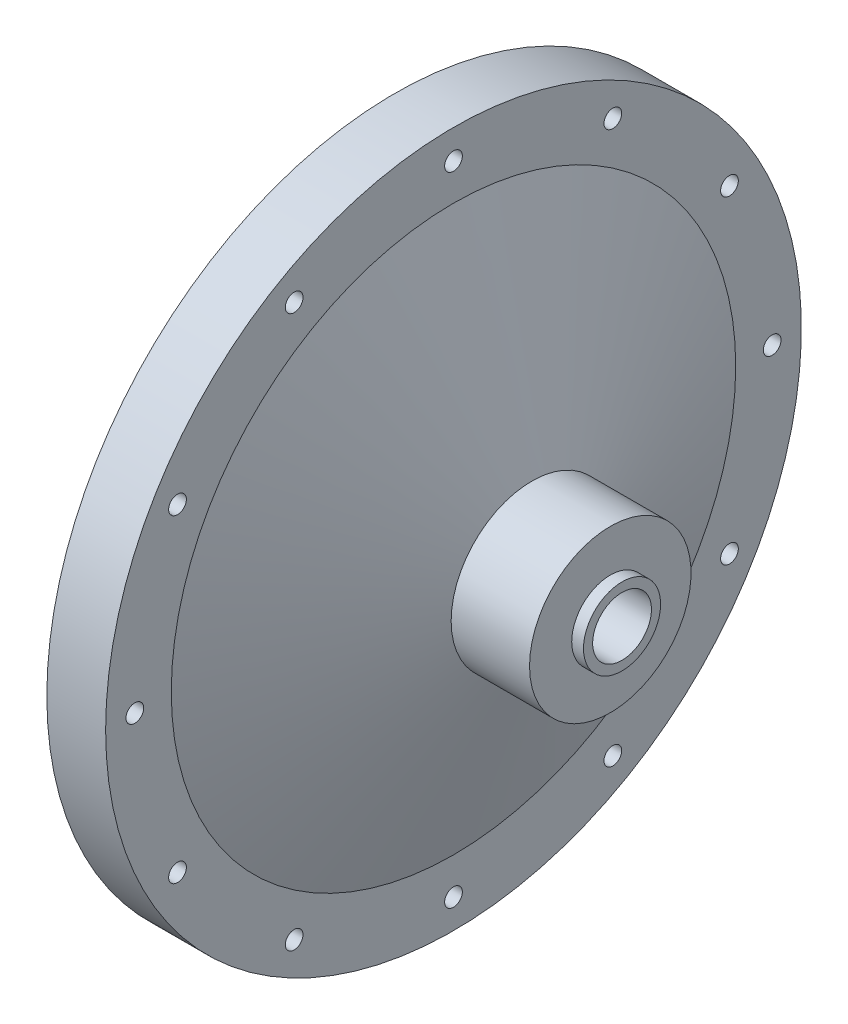
SolidWorks part; units mm, degrees
material "7075-T6 (SN)"
ref_plane "Front Plane" through (0, 0, 0) normal (0, 0, 1) x (1, 0, 0)
ref_plane "Top Plane" through (0, 0, 0) normal (0, 1, 0) x (1, 0, 0)
ref_plane "Right Plane" through (0, 0, 0) normal (1, 0, 0) x (0, 0, -1)
sketch "Sketch2" plane through (0, 0, 0) normal (0, 0, 1) x (1, 0, 0)
  line L0 (0, 0) -> (165.0115, 0) construction
  line L1 (0, 0) -> (0, 56.3562)
  line L2 (0, 56.3562) -> (9.525, 56.3562)
  line L3 (9.525, 56.3562) -> (9.525, 45.72)
  line L4 (9.525, 45.72) -> (22.225, 13.081)
  line L5 (34.925, 13.081) -> (34.925, 6.2484)
  line L6 (22.225, 13.081) -> (34.925, 13.081)
  line L7 (34.925, 6.2484) -> (36.83, 6.2484)
  line L8 (36.83, 6.2484) -> (36.83, 0)
  line L9 (0, 0) -> (36.83, 0)
  dimension "D1" = 56.3562
  dimension "D2" = 9.525
  dimension "D3" = 45.72
  dimension "D4" = 13.081
  dimension "D5" = 12.7
  dimension "D6" = 12.7
  dimension "D7" = 6.2484
  dimension "D8" = 1.905
revolve "Main Structure" add sketch "Sketch2" angle 360 about L0
cosmetic thread "Cosmetic Thread1" parameters "D2"=23.1953
sketch "Sketch3" plane through (36.83, 0, 0) normal (1, 0, 0) x (0, 0, -1)
  circle A0 centre (0, 0) radius 4.7625
  dimension "D1" = 9.525
extrude "Oxidizer Inlet Hole" cut sketch "Sketch3" against normal through all
sketch "Sketch4" plane through (0, 0, 0) normal (-1, 0, 0) x (0, 0, 1)
  circle A0 centre (0, 0) radius 51.6255 construction
  circle A1 centre (0, -51.6255) radius 2.146
  circle A2 centre (-25.8127, -44.709) radius 2.146
  circle A3 centre (-44.709, -25.8128) radius 2.146
  circle A4 centre (-51.6255, 0) radius 2.146
  circle A5 centre (-44.709, 25.8127) radius 2.146
  circle A6 centre (-25.8128, 44.709) radius 2.146
  circle A7 centre (0, 51.6255) radius 2.146
  circle A8 centre (25.8127, 44.709) radius 2.146
  circle A9 centre (44.709, 25.8128) radius 2.146
  circle A10 centre (51.6255, 0) radius 2.146
  circle A11 centre (44.709, -25.8127) radius 2.146
  circle A12 centre (25.8128, -44.709) radius 2.146
  point P29 (0, 0)
  dimension "D1" = 12
  dimension "D2" = 103.251
hole_wizard "Flange Holes" positions "Sketch7" profile "Sketch8" hole size "#33" standard "ANSI Inch" end condition up to next
sketch "Sketch7" plane through (0, 0, 0) normal (-1, 0, 0) x (0, 0, 1)
  point P0 (0, -51.6255)
  point P3 (-25.8127, -44.709)
  point P6 (-44.709, -25.8128)
  point P9 (-51.6255, 0)
  point P12 (-44.709, 25.8127)
  point P15 (-25.8128, 44.709)
  point P18 (0, 51.6255)
  point P21 (25.8127, 44.709)
  point P24 (44.709, 25.8128)
  point P27 (51.6255, 0)
  point P30 (44.709, -25.8127)
  point P33 (25.8128, -44.709)
sketch "Sketch8" plane through (0, -51.6255, 0) normal (0, 1, 0) x (0, 0, 1)
  line L0 (0, 0) -> (0, 9.525)
  line L1 (0, 9.525) -> (1.4351, 9.525)
  line L2 (1.4351, 9.525) -> (1.4351, 0)
  line L5 (1.4351, 0) -> (0, 0)
  line L11 (0, -6.35) -> (0, 107.95) construction
  dimension "Thru Hole Dia." = 2.8702
  dimension "Thru Hole Depth" = 9.525
sketch "Sketch9" plane through (0, 0, 0) normal (-1, 0, 0) x (0, 0, 1)
  line L0 (0, 0) -> (-67.6727, 18.1329) construction
  line L1 (0, 0) -> (-51.6255, 0) construction
  circle A0 centre (0, 0) radius 51.6255 construction
  circle A1 centre (-49.8664, 13.3617) radius 2.9451
  circle A2 centre (49.8664, -13.3617) radius 2.9451
  point P14 (0, 0)
  dimension "D1" = 15
  dimension "D2" = 2
hole_wizard "Dowel Holes" positions "Sketch10" profile "Sketch11" hole size "3/16" standard "ANSI Inch"
sketch "Sketch10" plane through (0, 0, 0) normal (-1, 0, 0) x (0, 0, 1)
  point P0 (49.8664, -13.3617)
  point P3 (-49.8664, 13.3617)
sketch "Sketch11" plane through (0, -13.3617, 49.8664) normal (0, 1, 0) x (0, 0, 1)
  line L0 (0, 0) -> (0, 7.7808)
  line L1 (0, 7.7808) -> (2.3812, 6.35)
  line L2 (2.3812, 6.35) -> (2.3812, 0)
  line L5 (2.3812, 0) -> (0, 0)
  line L10 (0, 7.7808) -> (-2.3812, 6.35) construction
  line L11 (0, -6.35) -> (0, 107.95) construction
  dimension "Hole Dia." = 4.7625
  dimension "Hole Depth" = 6.35
  dimension "Drill Angle" = 118
sketch "Sketch12" plane through (0, 0, 0) normal (-1, 0, 0) x (0, 0, 1)
  circle A0 centre (0, 0) radius 38.1
  dimension "D1" = 76.2
extrude "Impinging Plate Flat Cut" cut sketch "Sketch12" against normal blind 3.81
sketch "Sketch21" plane through (0, 0, 0) normal (-1, 0, 0) x (0, 0, 1)
  circle A0 centre (0, 0) radius 44.45
  circle A2 centre (0, 51.6255) radius 1.4351
  circle A3 centre (51.6255, 0) radius 1.4351
  circle A4 centre (0, -51.6255) radius 1.4351
  circle A5 centre (-51.6255, 0) radius 1.4351
  point P16 (0, 0)
  dimension "D1" = 88.9
  dimension "D2" = 4
ref_plane "Plane1" through (6.35, 0, 0) normal (-1, 0, 0) x (0, 0, 1)
sketch "Sketch14" plane through (3.81, 0, 0) normal (-1, 0, 0) x (0, 0, 1)
  circle A0 centre (0, 0) radius 38.1
  dimension "D1" = 76.2
sketch "Sketch15" plane through (6.35, 0, 0) normal (-1, 0, 0) x (0, 0, 1)
  circle A0 centre (0, 0) radius 38.1
  dimension "D1" = 76.2
loft "Impinging Plate Taper Cut" cut profiles "Sketch14", "Sketch15"
sketch "Sketch16" plane through (6.35, 0, 0) normal (-1, 0, 0) x (0, 0, 1)
  circle A0 centre (0, 0) radius 28.575
  dimension "D1" = 57.15
ref_plane "Plane2" through (21.59, 0, 0) normal (-1, 0, 0) x (0, 0, 1)
sketch "Sketch17" plane through (21.59, 0, 0) normal (-1, 0, 0) x (0, 0, 1)
  circle A0 centre (0, 0) radius 4.7625
  dimension "D1" = 9.525
loft "Internal Flow Path Loft Cut" cut profiles "Sketch16", "Sketch17"
fillet "Internal Fillet" radius 3.175 1 edges at (21.59, 0, 4.7625)
sketch "Sketch18" plane through (6.35, 0, 0) normal (-1, 0, 0) x (0, 0, 1)
  circle A0 centre (0, 0) radius 33.3375
  circle A1 centre (33.3375, 0) radius 1.5042
  dimension "D1" = 66.675
hole_wizard "4-40 Tapped Holes " positions "Sketch19" profile "Sketch20" hole size "#4-40" standard "ANSI Inch"
sketch "Sketch19" plane through (6.35, 0, 0) normal (-1, 0, 0) x (0, 0, 1)
  point P0 (33.3375, 0)
sketch "Sketch20" plane through (6.35, 0, 33.3375) normal (0, 1, 0) x (0, 0, 1)
  line L0 (0, 0) -> (0, 3.8542)
  line L1 (0, 3.8542) -> (1.1303, 3.175)
  line L2 (1.1303, 3.175) -> (1.1303, 0)
  line L5 (1.1303, 0) -> (0, 0)
  line L10 (0, 3.8542) -> (-1.1303, 3.175) construction
  line L11 (0, -6.35) -> (0, 107.95) construction
  dimension "Hole Dia." = 2.2606
  dimension "Hole Depth" = 3.175
  dimension "Drill Angle" = 118
pattern_circular "Extended 8 BC" count 8 over 360 about axis through (0, 0, 0) along (1, 0, 0) of "4-40 Tapped Holes "
chamfer "Chamfer for Impinging Edge" distance 0.127 angle 45 1 edges at (6.35, 0, 38.1)
